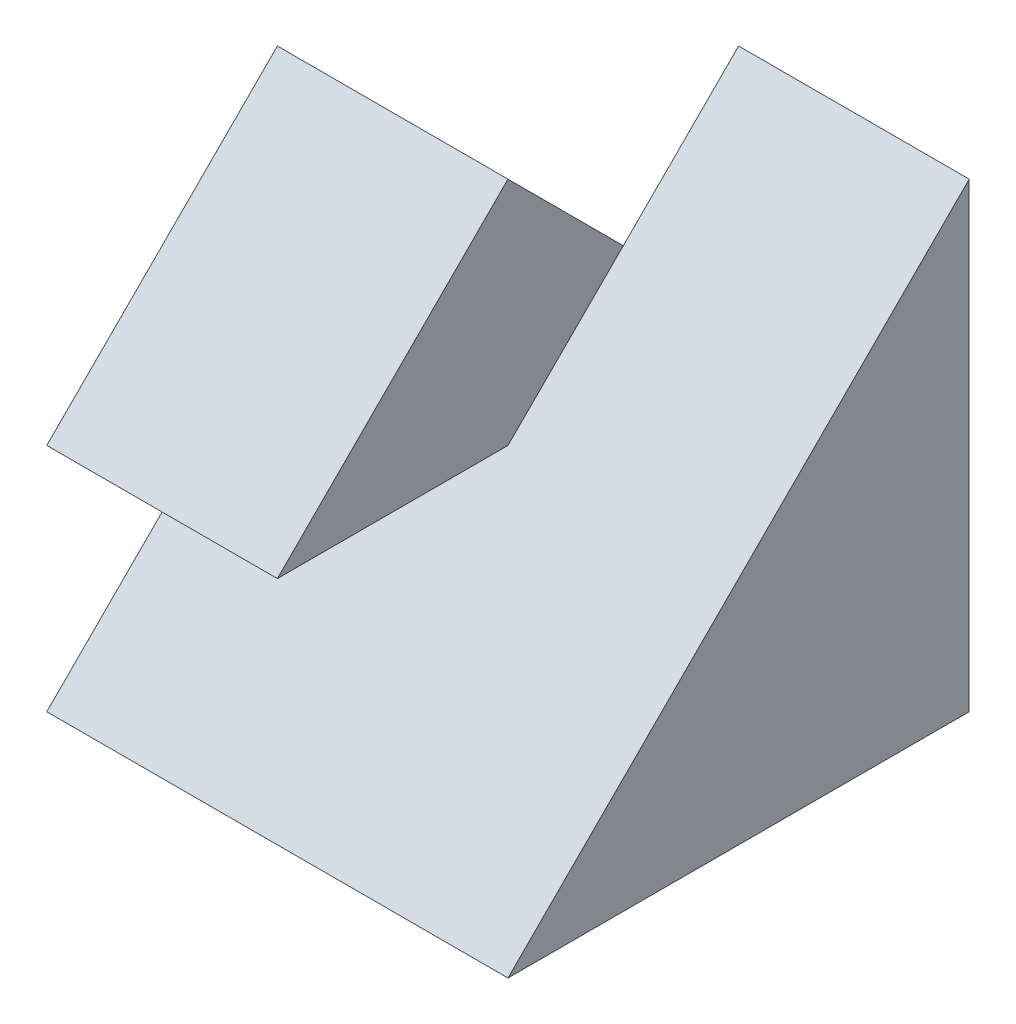
SolidWorks part; units mm, degrees
ref_plane "Front" through (0, 0, 0) normal (0, 0, 1) x (1, 0, 0)
ref_plane "Top" through (0, 0, 0) normal (0, 1, 0) x (1, 0, 0)
ref_plane "Right" through (0, 0, 0) normal (1, 0, 0) x (0, 0, -1)
sketch "Sketch1" plane through (0, 0, 0) normal (0, 1, 0) x (1, 0, 0)
  line L1 (-2, -2) -> (2, -2)
  line L2 (-2, -2) -> (-2, 2)
  line L3 (-2, 2) -> (2, 2)
  line L4 (2, -2) -> (2, 2)
  line L5 (-2, -2) -> (2, 2) construction
  line L6 (-2, 2) -> (2, -2) construction
  point P0 (0, 0)
  dimension "D1" = 4
  dimension "D2" = 4
extrude "Boss-Extrude1" add sketch "Sketch1" along normal blind 4
sketch "Sketch2" plane through (-2, 0, 0) normal (-1, 0, 0) x (0, 0, 1)
  line L0 (2, 0) -> (0, 2)
  line L1 (0, 2) -> (2, 2)
  line L2 (2, 4) -> (2, 0) construction
  line L3 (2, 2) -> (0, 4)
  line L4 (-2, 4) -> (2, 4) construction
  line L5 (0, 4) -> (2, 4)
  line L6 (2, 4) -> (2, 0)
  line L7 (0, 4) -> (-2, 2)
  line L8 (-2, 4) -> (-2, 0) construction
  line L9 (-2, 2) -> (-2, 4)
  line L10 (-2, 4) -> (0, 4)
  line M2 (2, 0) -> (2, 4)
  line M3 (2, 4) -> (-2, 4)
extrude "Cut-Extrude1" cut sketch "Sketch2" against normal blind 2 contours L1 L0 M2 | L3 M2 M3 | L7 L9 L10
sketch "Sketch3" plane through (2, 0, 0) normal (1, 0, 0) x (0, 0, -1)
  line L0 (-2, 0) -> (2, 4)
  line L1 (2, 4) -> (-2, 4.1166)
  line L2 (-2, 4.1166) -> (-2, 0)
extrude "Cut-Extrude2" cut sketch "Sketch3" against normal blind 2
